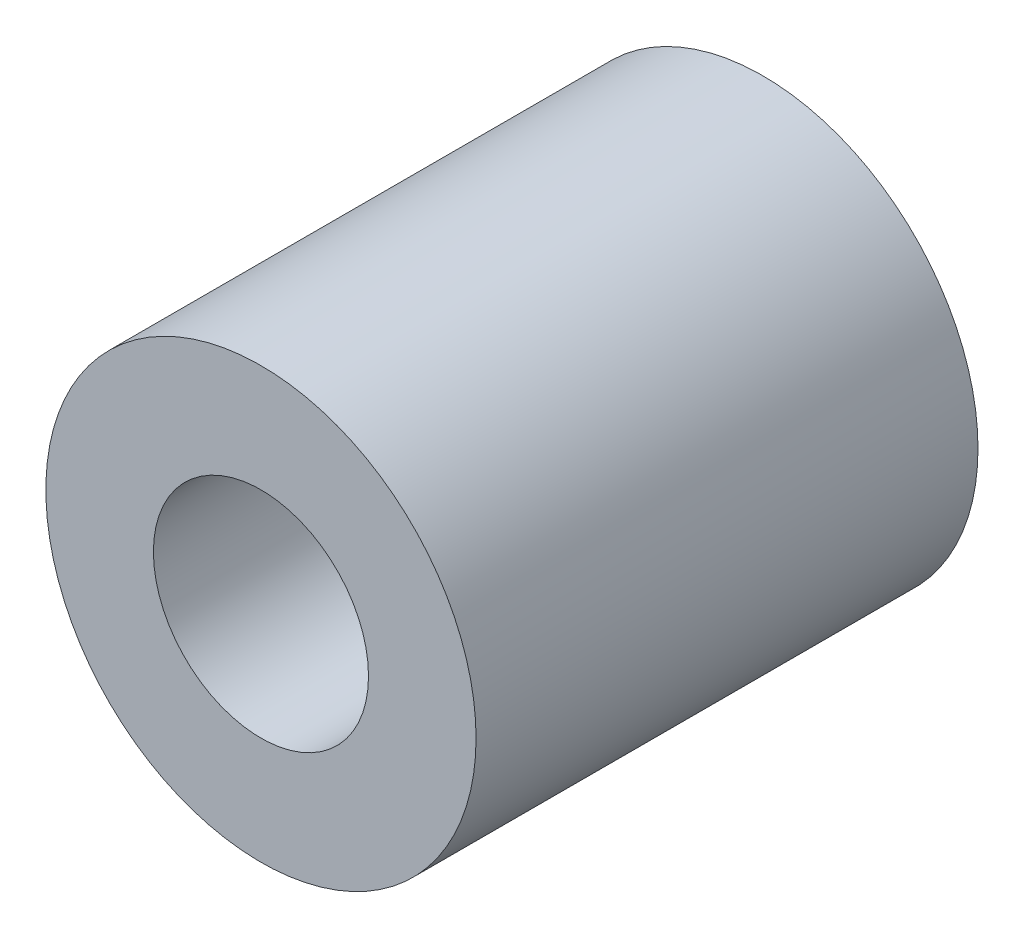
SolidWorks part; units mm, degrees
ref_plane "Front Plane" through (0, 0, 0) normal (0, 0, 1) x (1, 0, 0)
ref_plane "Top Plane" through (0, 0, 0) normal (0, 1, 0) x (1, 0, 0)
ref_plane "Right Plane" through (0, 0, 0) normal (1, 0, 0) x (0, 0, -1)
sketch "Sketch1" plane through (0, 0, 0) normal (0, 0, 1) x (1, 0, 0)
  circle A0 centre (0, 0) radius 15
  circle A1 centre (0, 0) radius 6
  dimension "D1" = 30
  dimension "D2" = 12
extrude "Boss-Extrude1" add sketch "Sketch1" along normal blind 35
sketch "Sketch2" plane through (0, 0, 35) normal (0, 0, 1) x (1, 0, 0)
  circle A0 centre (0, 0) radius 7.5
  dimension "D1" = 15
extrude "Cut-Extrude1" cut sketch "Sketch2" against normal mid plane 35
